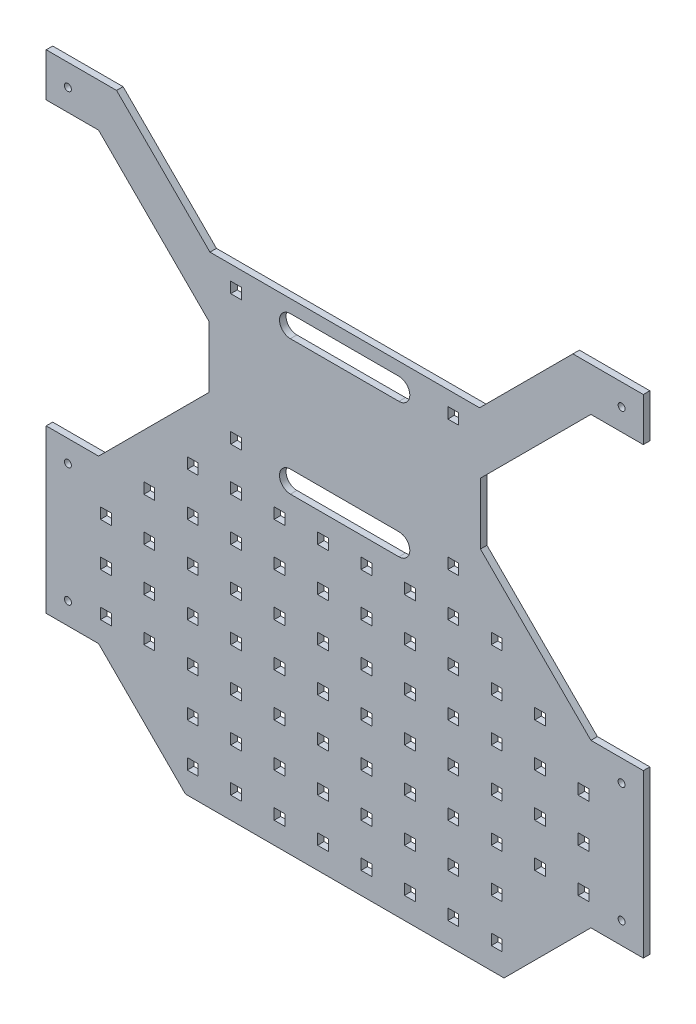
SolidWorks part; units mm, degrees
material "ABS"
ref_plane "Front Plane" through (0, 0, 0) normal (0, 0, 1) x (1, 0, 0)
ref_plane "Top Plane" through (0, 0, 0) normal (0, 1, 0) x (1, 0, 0)
ref_plane "Right Plane" through (0, 0, 0) normal (1, 0, 0) x (0, 0, -1)
sketch "Sketch1" plane through (0, 0, 0) normal (0, 0, 1) x (1, 0, 0)
  line L0 (-21.5101, 357.497) -> (2.6321, 357.497)
  line L1 (-21.5101, 592.497) -> (-21.5101, 302.497) construction
  line L2 (-21.5101, 442.2845) -> (-1.5101, 442.2845) construction
  line L3 (2.6321, 357.497) -> (53.4899, 306.6392)
  line L4 (185.9899, 432.2845) -> (165.9899, 412.2845)
  line L5 (43.4899, 292.497) -> (188.4899, 292.497) construction
  line L6 (43.4899, 282.497) -> (43.4899, 302.497) construction
  line L7 (188.4899, 302.497) -> (188.4899, 282.497) construction
  line L8 (115.9899, 412.2845) -> (115.9899, 208.7129) construction
  line L9 (53.4899, 306.6392) -> (53.4899, 278.3549)
  line L10 (-21.5101, 357.497) -> (-21.5101, 432.2845)
  line L11 (-21.5101, 432.2845) -> (45.9899, 432.2845)
  line L12 (45.9899, 432.2845) -> (65.9899, 412.2845)
  line L13 (65.9899, 412.2845) -> (165.9899, 412.2845)
  line L14 (-1.5101, 347.497) -> (-180.6113, 347.497) construction
  line L15 (43.4899, 302.497) -> (-1.5101, 347.497) construction
  line L16 (253.4899, 432.2845) -> (185.9899, 432.2845)
  line L17 (253.4899, 357.497) -> (253.4899, 432.2845)
  line L18 (178.4899, 306.6392) -> (178.4899, 278.3549)
  line L19 (229.3478, 357.497) -> (178.4899, 306.6392)
  line L20 (253.4899, 357.497) -> (229.3478, 357.497)
  line L21 (253.4899, 227.497) -> (229.3478, 227.497)
  line L22 (229.3478, 227.497) -> (178.4899, 278.3549)
  line L23 (253.4899, 227.497) -> (253.4899, 152.7096)
  line L24 (253.4899, 152.7096) -> (229.3478, 152.7096)
  line L27 (-21.5101, 152.7096) -> (2.6321, 152.7096)
  line L28 (-21.5101, 227.497) -> (-21.5101, 152.7096)
  line L30 (2.6321, 227.497) -> (53.4899, 278.3549)
  line L31 (-21.5101, 227.497) -> (2.6321, 227.497)
  line L32 (2.6321, 152.7096) -> (42.6321, 112.7096)
  line L33 (42.6321, 112.7096) -> (189.3478, 112.7096)
  line L34 (189.3478, 112.7096) -> (229.3478, 152.7096)
  line L35 (2.6321, 152.7096) -> (2.6321, 432.2845) construction
  line L36 (229.3478, 152.7096) -> (229.3478, 432.2845) construction
  point P39 (178.4899, 292.497)
  point P47 (53.4899, 292.497)
  dimension "D1" = 10
  dimension "D2" = 10
  dimension "D3" = 10
  dimension "D4" = 10
  dimension "D5" = 20
  dimension "D6" = 50
  dimension "D7" = 72.5
  dimension "D8" = 45
  dimension "D9" = 45
  dimension "D10" = 40
extrude "Extrude1" add sketch "Sketch1" along normal blind 3
sketch "Sketch3" plane through (0, 0, 3) normal (0, 0, 1) x (1, 0, 0)
  line L0 (43.4899, 292.497) -> (188.4899, 292.497) construction
  line L1 (43.4899, 282.497) -> (43.4899, 302.497) construction
  line L2 (188.4899, 302.497) -> (188.4899, 282.497) construction
  line L3 (90.9488, 323.497) -> (140.9488, 323.497) construction
  line L4 (90.9488, 328.497) -> (140.9488, 328.497)
  line L5 (90.9488, 318.497) -> (140.9488, 318.497)
  line L6 (90.9488, 261.497) -> (140.9488, 261.497) construction
  line L7 (90.9488, 256.497) -> (140.9488, 256.497)
  line L8 (90.9488, 266.497) -> (140.9488, 266.497)
  arc A0 (90.9488, 328.497) -> (90.9488, 318.497) centre (90.9488, 323.497) ccw
  arc A1 (140.9488, 318.497) -> (140.9488, 328.497) centre (140.9488, 323.497) ccw
  arc A2 (90.9488, 256.497) -> (90.9488, 266.497) centre (90.9488, 261.497) cw
  arc A3 (140.9488, 266.497) -> (140.9488, 256.497) centre (140.9488, 261.497) cw
  point P8 (115.9488, 323.497)
  point P15 (115.9488, 261.497)
  dimension "D3" = 5
  dimension "D1" = 31
  dimension "D2" = 50
extrude "Cut-Extrude2" cut sketch "Sketch3" against normal blind 3
sketch "Sketch5" plane through (0, 0, 0) normal (0, 0, -1) x (-1, 0, 0)
  line L0 (-253.4899, 377.497) -> (-221.0635, 377.497)
  line L1 (-253.4899, 357.497) -> (-253.4899, 432.2845) construction
  line L2 (-221.0635, 377.497) -> (-178.0635, 334.497)
  line L3 (-178.0635, 334.497) -> (-53.9163, 334.497)
  line L4 (-53.9163, 334.497) -> (-10.9163, 377.497)
  line L5 (-10.9163, 377.497) -> (21.5101, 377.497)
  line L6 (21.5101, 432.2845) -> (21.5101, 357.497) construction
  line L7 (-229.3478, 357.497) -> (-253.4899, 357.497) construction
  line L8 (-178.4899, 306.6392) -> (-229.3478, 357.497) construction
  line L9 (-2.6321, 357.497) -> (-53.4899, 306.6392) construction
  line L10 (21.5101, 357.497) -> (-2.6321, 357.497) construction
  line L11 (-90.9488, 318.497) -> (-140.9488, 318.497) construction
  line L12 (-253.4899, 377.497) -> (-253.4899, 432.2845)
  line L13 (-253.4899, 432.2845) -> (21.5101, 432.2845)
  line L14 (21.5101, 432.2845) -> (21.5101, 377.497)
  dimension "D1" = 20
  dimension "D2" = 20
  dimension "D3" = 20
  dimension "D4" = 20
  dimension "D5" = 16
extrude "Extrude3" cut sketch "Sketch5" against normal blind 10
sketch "Sketch6" plane through (0, 0, 3) normal (0, 0, 1) x (1, 0, 0)
  line L0 (-11.5101, 377.497) -> (-11.5101, 152.7096) construction
  line L1 (10.9163, 377.497) -> (-21.5101, 377.497) construction
  line L2 (-21.5101, 152.7096) -> (2.6321, 152.7096) construction
  line L3 (115.9899, 334.497) -> (115.9899, 112.7096) construction
  line L4 (178.0635, 334.497) -> (53.9163, 334.497) construction
  line L5 (42.6321, 112.7096) -> (189.3478, 112.7096) construction
  line L6 (2.6321, 227.497) -> (-21.5101, 227.497) construction
  line L7 (-21.5101, 227.497) -> (-21.5101, 152.7096) construction
  circle A0 centre (-11.5101, 367.497) radius 1.6
  circle A1 centre (-11.5101, 217.497) radius 1.6
  circle A2 centre (-11.5101, 162.7096) radius 1.6
  circle A3 centre (243.4899, 162.7096) radius 1.6
  circle A4 centre (243.4899, 217.497) radius 1.6
  circle A5 centre (243.4899, 367.497) radius 1.6
  dimension "D1" = 10
  dimension "D2" = 10
  dimension "D3" = 10
  dimension "D4" = 3.2
  dimension "D5" = 10
extrude "Extrude4" cut sketch "Sketch6" against normal blind 50
sketch "Sketch7" plane through (0, 0, 3) normal (0, 0, 1) x (1, 0, 0)
  line L10 (43.4899, 127.7096) -> (48.4899, 127.7096)
  line L11 (43.4899, 127.7096) -> (43.4899, 122.7096)
  line L12 (43.4899, 122.7096) -> (48.4899, 122.7096)
  line L13 (48.4899, 127.7096) -> (48.4899, 122.7096)
  line L14 (63.4899, 127.7096) -> (68.4899, 127.7096)
  line L15 (63.4899, 127.7096) -> (63.4899, 122.7096)
  line L16 (63.4899, 122.7096) -> (68.4899, 122.7096)
  line L17 (68.4899, 127.7096) -> (68.4899, 122.7096)
  line L18 (83.4899, 127.7096) -> (88.4899, 127.7096)
  line L19 (83.4899, 127.7096) -> (83.4899, 122.7096)
  line L20 (83.4899, 122.7096) -> (88.4899, 122.7096)
  line L21 (88.4899, 127.7096) -> (88.4899, 122.7096)
  line L22 (103.4899, 127.7096) -> (108.4899, 127.7096)
  line L23 (103.4899, 127.7096) -> (103.4899, 122.7096)
  line L24 (103.4899, 122.7096) -> (108.4899, 122.7096)
  line L25 (108.4899, 127.7096) -> (108.4899, 122.7096)
  line L26 (123.4899, 127.7096) -> (128.4899, 127.7096)
  line L27 (123.4899, 127.7096) -> (123.4899, 122.7096)
  line L28 (123.4899, 122.7096) -> (128.4899, 122.7096)
  line L29 (128.4899, 127.7096) -> (128.4899, 122.7096)
  line L30 (143.4899, 127.7096) -> (148.4899, 127.7096)
  line L31 (143.4899, 127.7096) -> (143.4899, 122.7096)
  line L32 (143.4899, 122.7096) -> (148.4899, 122.7096)
  line L33 (148.4899, 127.7096) -> (148.4899, 122.7096)
  line L34 (163.4899, 127.7096) -> (168.4899, 127.7096)
  line L35 (163.4899, 127.7096) -> (163.4899, 122.7096)
  line L36 (163.4899, 122.7096) -> (168.4899, 122.7096)
  line L37 (168.4899, 127.7096) -> (168.4899, 122.7096)
  line L38 (183.4899, 127.7096) -> (188.4899, 127.7096)
  line L39 (183.4899, 127.7096) -> (183.4899, 122.7096)
  line L40 (183.4899, 122.7096) -> (188.4899, 122.7096)
  line L41 (188.4899, 127.7096) -> (188.4899, 122.7096)
  line L54 (43.4899, 147.7096) -> (48.4899, 147.7096)
  line L55 (43.4899, 147.7096) -> (43.4899, 142.7096)
  line L56 (43.4899, 142.7096) -> (48.4899, 142.7096)
  line L57 (48.4899, 147.7096) -> (48.4899, 142.7096)
  line L58 (63.4899, 147.7096) -> (68.4899, 147.7096)
  line L59 (63.4899, 147.7096) -> (63.4899, 142.7096)
  line L60 (63.4899, 142.7096) -> (68.4899, 142.7096)
  line L61 (68.4899, 147.7096) -> (68.4899, 142.7096)
  line L62 (83.4899, 147.7096) -> (88.4899, 147.7096)
  line L63 (83.4899, 147.7096) -> (83.4899, 142.7096)
  line L64 (83.4899, 142.7096) -> (88.4899, 142.7096)
  line L65 (88.4899, 147.7096) -> (88.4899, 142.7096)
  line L66 (103.4899, 147.7096) -> (108.4899, 147.7096)
  line L67 (103.4899, 147.7096) -> (103.4899, 142.7096)
  line L68 (103.4899, 142.7096) -> (108.4899, 142.7096)
  line L69 (108.4899, 147.7096) -> (108.4899, 142.7096)
  line L70 (123.4899, 147.7096) -> (128.4899, 147.7096)
  line L71 (123.4899, 147.7096) -> (123.4899, 142.7096)
  line L72 (123.4899, 142.7096) -> (128.4899, 142.7096)
  line L73 (128.4899, 147.7096) -> (128.4899, 142.7096)
  line L74 (143.4899, 147.7096) -> (148.4899, 147.7096)
  line L75 (143.4899, 147.7096) -> (143.4899, 142.7096)
  line L76 (143.4899, 142.7096) -> (148.4899, 142.7096)
  line L77 (148.4899, 147.7096) -> (148.4899, 142.7096)
  line L78 (163.4899, 147.7096) -> (168.4899, 147.7096)
  line L79 (163.4899, 147.7096) -> (163.4899, 142.7096)
  line L80 (163.4899, 142.7096) -> (168.4899, 142.7096)
  line L81 (168.4899, 147.7096) -> (168.4899, 142.7096)
  line L82 (183.4899, 147.7096) -> (188.4899, 147.7096)
  line L83 (183.4899, 147.7096) -> (183.4899, 142.7096)
  line L84 (183.4899, 142.7096) -> (188.4899, 142.7096)
  line L85 (188.4899, 147.7096) -> (188.4899, 142.7096)
  line L94 (23.4899, 167.7096) -> (28.4899, 167.7096)
  line L95 (23.4899, 167.7096) -> (23.4899, 162.7096)
  line L96 (23.4899, 162.7096) -> (28.4899, 162.7096)
  line L97 (28.4899, 167.7096) -> (28.4899, 162.7096)
  line L98 (43.4899, 167.7096) -> (48.4899, 167.7096)
  line L99 (43.4899, 167.7096) -> (43.4899, 162.7096)
  line L100 (43.4899, 162.7096) -> (48.4899, 162.7096)
  line L101 (48.4899, 167.7096) -> (48.4899, 162.7096)
  line L102 (63.4899, 167.7096) -> (68.4899, 167.7096)
  line L103 (63.4899, 167.7096) -> (63.4899, 162.7096)
  line L104 (63.4899, 162.7096) -> (68.4899, 162.7096)
  line L105 (68.4899, 167.7096) -> (68.4899, 162.7096)
  line L106 (83.4899, 167.7096) -> (88.4899, 167.7096)
  line L107 (83.4899, 167.7096) -> (83.4899, 162.7096)
  line L108 (83.4899, 162.7096) -> (88.4899, 162.7096)
  line L109 (88.4899, 167.7096) -> (88.4899, 162.7096)
  line L110 (103.4899, 167.7096) -> (108.4899, 167.7096)
  line L111 (103.4899, 167.7096) -> (103.4899, 162.7096)
  line L112 (103.4899, 162.7096) -> (108.4899, 162.7096)
  line L113 (108.4899, 167.7096) -> (108.4899, 162.7096)
  line L114 (123.4899, 167.7096) -> (128.4899, 167.7096)
  line L115 (123.4899, 167.7096) -> (123.4899, 162.7096)
  line L116 (123.4899, 162.7096) -> (128.4899, 162.7096)
  line L117 (128.4899, 167.7096) -> (128.4899, 162.7096)
  line L118 (143.4899, 167.7096) -> (148.4899, 167.7096)
  line L119 (143.4899, 167.7096) -> (143.4899, 162.7096)
  line L120 (143.4899, 162.7096) -> (148.4899, 162.7096)
  line L121 (148.4899, 167.7096) -> (148.4899, 162.7096)
  line L122 (163.4899, 167.7096) -> (168.4899, 167.7096)
  line L123 (163.4899, 167.7096) -> (163.4899, 162.7096)
  line L124 (163.4899, 162.7096) -> (168.4899, 162.7096)
  line L125 (168.4899, 167.7096) -> (168.4899, 162.7096)
  line L126 (183.4899, 167.7096) -> (188.4899, 167.7096)
  line L127 (183.4899, 167.7096) -> (183.4899, 162.7096)
  line L128 (183.4899, 162.7096) -> (188.4899, 162.7096)
  line L129 (188.4899, 167.7096) -> (188.4899, 162.7096)
  line L130 (203.4899, 167.7096) -> (208.4899, 167.7096)
  line L131 (203.4899, 167.7096) -> (203.4899, 162.7096)
  line L132 (203.4899, 162.7096) -> (208.4899, 162.7096)
  line L133 (208.4899, 167.7096) -> (208.4899, 162.7096)
  line L134 (223.4899, 167.7096) -> (228.4899, 167.7096)
  line L135 (223.4899, 167.7096) -> (223.4899, 162.7096)
  line L136 (223.4899, 162.7096) -> (228.4899, 162.7096)
  line L137 (228.4899, 167.7096) -> (228.4899, 162.7096)
  line L138 (23.4899, 187.7096) -> (28.4899, 187.7096)
  line L139 (23.4899, 187.7096) -> (23.4899, 182.7096)
  line L140 (23.4899, 182.7096) -> (28.4899, 182.7096)
  line L141 (28.4899, 187.7096) -> (28.4899, 182.7096)
  line L142 (43.4899, 187.7096) -> (48.4899, 187.7096)
  line L143 (43.4899, 187.7096) -> (43.4899, 182.7096)
  line L144 (43.4899, 182.7096) -> (48.4899, 182.7096)
  line L145 (48.4899, 187.7096) -> (48.4899, 182.7096)
  line L146 (63.4899, 187.7096) -> (68.4899, 187.7096)
  line L147 (63.4899, 187.7096) -> (63.4899, 182.7096)
  line L148 (63.4899, 182.7096) -> (68.4899, 182.7096)
  line L149 (68.4899, 187.7096) -> (68.4899, 182.7096)
  line L150 (83.4899, 187.7096) -> (88.4899, 187.7096)
  line L151 (83.4899, 187.7096) -> (83.4899, 182.7096)
  line L152 (83.4899, 182.7096) -> (88.4899, 182.7096)
  line L153 (88.4899, 187.7096) -> (88.4899, 182.7096)
  line L154 (103.4899, 187.7096) -> (108.4899, 187.7096)
  line L155 (103.4899, 187.7096) -> (103.4899, 182.7096)
  line L156 (103.4899, 182.7096) -> (108.4899, 182.7096)
  line L157 (108.4899, 187.7096) -> (108.4899, 182.7096)
  line L158 (123.4899, 187.7096) -> (128.4899, 187.7096)
  line L159 (123.4899, 187.7096) -> (123.4899, 182.7096)
  line L160 (123.4899, 182.7096) -> (128.4899, 182.7096)
  line L161 (128.4899, 187.7096) -> (128.4899, 182.7096)
  line L162 (143.4899, 187.7096) -> (148.4899, 187.7096)
  line L163 (143.4899, 187.7096) -> (143.4899, 182.7096)
  line L164 (143.4899, 182.7096) -> (148.4899, 182.7096)
  line L165 (148.4899, 187.7096) -> (148.4899, 182.7096)
  line L166 (163.4899, 187.7096) -> (168.4899, 187.7096)
  line L167 (163.4899, 187.7096) -> (163.4899, 182.7096)
  line L168 (163.4899, 182.7096) -> (168.4899, 182.7096)
  line L169 (168.4899, 187.7096) -> (168.4899, 182.7096)
  line L170 (183.4899, 187.7096) -> (188.4899, 187.7096)
  line L171 (183.4899, 187.7096) -> (183.4899, 182.7096)
  line L172 (183.4899, 182.7096) -> (188.4899, 182.7096)
  line L173 (188.4899, 187.7096) -> (188.4899, 182.7096)
  line L174 (203.4899, 187.7096) -> (208.4899, 187.7096)
  line L175 (203.4899, 187.7096) -> (203.4899, 182.7096)
  line L176 (203.4899, 182.7096) -> (208.4899, 182.7096)
  line L177 (208.4899, 187.7096) -> (208.4899, 182.7096)
  line L178 (223.4899, 187.7096) -> (228.4899, 187.7096)
  line L179 (223.4899, 187.7096) -> (223.4899, 182.7096)
  line L180 (223.4899, 182.7096) -> (228.4899, 182.7096)
  line L181 (228.4899, 187.7096) -> (228.4899, 182.7096)
  line L182 (23.4899, 207.7096) -> (28.4899, 207.7096)
  line L183 (23.4899, 207.7096) -> (23.4899, 202.7096)
  line L184 (23.4899, 202.7096) -> (28.4899, 202.7096)
  line L185 (28.4899, 207.7096) -> (28.4899, 202.7096)
  line L186 (43.4899, 207.7096) -> (48.4899, 207.7096)
  line L187 (43.4899, 207.7096) -> (43.4899, 202.7096)
  line L188 (43.4899, 202.7096) -> (48.4899, 202.7096)
  line L189 (48.4899, 207.7096) -> (48.4899, 202.7096)
  line L190 (63.4899, 207.7096) -> (68.4899, 207.7096)
  line L191 (63.4899, 207.7096) -> (63.4899, 202.7096)
  line L192 (63.4899, 202.7096) -> (68.4899, 202.7096)
  line L193 (68.4899, 207.7096) -> (68.4899, 202.7096)
  line L194 (83.4899, 207.7096) -> (88.4899, 207.7096)
  line L195 (83.4899, 207.7096) -> (83.4899, 202.7096)
  line L196 (83.4899, 202.7096) -> (88.4899, 202.7096)
  line L197 (88.4899, 207.7096) -> (88.4899, 202.7096)
  line L198 (103.4899, 207.7096) -> (108.4899, 207.7096)
  line L199 (103.4899, 207.7096) -> (103.4899, 202.7096)
  line L200 (103.4899, 202.7096) -> (108.4899, 202.7096)
  line L201 (108.4899, 207.7096) -> (108.4899, 202.7096)
  line L202 (123.4899, 207.7096) -> (128.4899, 207.7096)
  line L203 (123.4899, 207.7096) -> (123.4899, 202.7096)
  line L204 (123.4899, 202.7096) -> (128.4899, 202.7096)
  line L205 (128.4899, 207.7096) -> (128.4899, 202.7096)
  line L206 (143.4899, 207.7096) -> (148.4899, 207.7096)
  line L207 (143.4899, 207.7096) -> (143.4899, 202.7096)
  line L208 (143.4899, 202.7096) -> (148.4899, 202.7096)
  line L209 (148.4899, 207.7096) -> (148.4899, 202.7096)
  line L210 (163.4899, 207.7096) -> (168.4899, 207.7096)
  line L211 (163.4899, 207.7096) -> (163.4899, 202.7096)
  line L212 (163.4899, 202.7096) -> (168.4899, 202.7096)
  line L213 (168.4899, 207.7096) -> (168.4899, 202.7096)
  line L214 (183.4899, 207.7096) -> (188.4899, 207.7096)
  line L215 (183.4899, 207.7096) -> (183.4899, 202.7096)
  line L216 (183.4899, 202.7096) -> (188.4899, 202.7096)
  line L217 (188.4899, 207.7096) -> (188.4899, 202.7096)
  line L218 (203.4899, 207.7096) -> (208.4899, 207.7096)
  line L219 (203.4899, 207.7096) -> (203.4899, 202.7096)
  line L220 (203.4899, 202.7096) -> (208.4899, 202.7096)
  line L221 (208.4899, 207.7096) -> (208.4899, 202.7096)
  line L222 (223.4899, 207.7096) -> (228.4899, 207.7096)
  line L223 (223.4899, 207.7096) -> (223.4899, 202.7096)
  line L224 (223.4899, 202.7096) -> (228.4899, 202.7096)
  line L225 (228.4899, 207.7096) -> (228.4899, 202.7096)
  line L226 (23.4899, 227.7096) -> (28.4899, 227.7096)
  line L227 (23.4899, 227.7096) -> (23.4899, 222.7096)
  line L228 (23.4899, 222.7096) -> (28.4899, 222.7096)
  line L229 (28.4899, 227.7096) -> (28.4899, 222.7096)
  line L230 (43.4899, 227.7096) -> (48.4899, 227.7096)
  line L231 (43.4899, 227.7096) -> (43.4899, 222.7096)
  line L232 (43.4899, 222.7096) -> (48.4899, 222.7096)
  line L233 (48.4899, 227.7096) -> (48.4899, 222.7096)
  line L234 (63.4899, 227.7096) -> (68.4899, 227.7096)
  line L235 (63.4899, 227.7096) -> (63.4899, 222.7096)
  line L236 (63.4899, 222.7096) -> (68.4899, 222.7096)
  line L237 (68.4899, 227.7096) -> (68.4899, 222.7096)
  line L238 (83.4899, 227.7096) -> (88.4899, 227.7096)
  line L239 (83.4899, 227.7096) -> (83.4899, 222.7096)
  line L240 (83.4899, 222.7096) -> (88.4899, 222.7096)
  line L241 (88.4899, 227.7096) -> (88.4899, 222.7096)
  line L242 (103.4899, 227.7096) -> (108.4899, 227.7096)
  line L243 (103.4899, 227.7096) -> (103.4899, 222.7096)
  line L244 (103.4899, 222.7096) -> (108.4899, 222.7096)
  line L245 (108.4899, 227.7096) -> (108.4899, 222.7096)
  line L246 (123.4899, 227.7096) -> (128.4899, 227.7096)
  line L247 (123.4899, 227.7096) -> (123.4899, 222.7096)
  line L248 (123.4899, 222.7096) -> (128.4899, 222.7096)
  line L249 (128.4899, 227.7096) -> (128.4899, 222.7096)
  line L250 (143.4899, 227.7096) -> (148.4899, 227.7096)
  line L251 (143.4899, 227.7096) -> (143.4899, 222.7096)
  line L252 (143.4899, 222.7096) -> (148.4899, 222.7096)
  line L253 (148.4899, 227.7096) -> (148.4899, 222.7096)
  line L254 (163.4899, 227.7096) -> (168.4899, 227.7096)
  line L255 (163.4899, 227.7096) -> (163.4899, 222.7096)
  line L256 (163.4899, 222.7096) -> (168.4899, 222.7096)
  line L257 (168.4899, 227.7096) -> (168.4899, 222.7096)
  line L258 (183.4899, 227.7096) -> (188.4899, 227.7096)
  line L259 (183.4899, 227.7096) -> (183.4899, 222.7096)
  line L260 (183.4899, 222.7096) -> (188.4899, 222.7096)
  line L261 (188.4899, 227.7096) -> (188.4899, 222.7096)
  line L262 (203.4899, 227.7096) -> (208.4899, 227.7096)
  line L263 (203.4899, 227.7096) -> (203.4899, 222.7096)
  line L264 (203.4899, 222.7096) -> (208.4899, 222.7096)
  line L265 (208.4899, 227.7096) -> (208.4899, 222.7096)
  line L274 (43.4899, 247.7096) -> (48.4899, 247.7096)
  line L275 (43.4899, 247.7096) -> (43.4899, 242.7096)
  line L276 (43.4899, 242.7096) -> (48.4899, 242.7096)
  line L277 (48.4899, 247.7096) -> (48.4899, 242.7096)
  line L278 (63.4899, 247.7096) -> (68.4899, 247.7096)
  line L279 (63.4899, 247.7096) -> (63.4899, 242.7096)
  line L280 (63.4899, 242.7096) -> (68.4899, 242.7096)
  line L281 (68.4899, 247.7096) -> (68.4899, 242.7096)
  line L282 (83.4899, 247.7096) -> (88.4899, 247.7096)
  line L283 (83.4899, 247.7096) -> (83.4899, 242.7096)
  line L284 (83.4899, 242.7096) -> (88.4899, 242.7096)
  line L285 (88.4899, 247.7096) -> (88.4899, 242.7096)
  line L286 (103.4899, 247.7096) -> (108.4899, 247.7096)
  line L287 (103.4899, 247.7096) -> (103.4899, 242.7096)
  line L288 (103.4899, 242.7096) -> (108.4899, 242.7096)
  line L289 (108.4899, 247.7096) -> (108.4899, 242.7096)
  line L290 (123.4899, 247.7096) -> (128.4899, 247.7096)
  line L291 (123.4899, 247.7096) -> (123.4899, 242.7096)
  line L292 (123.4899, 242.7096) -> (128.4899, 242.7096)
  line L293 (128.4899, 247.7096) -> (128.4899, 242.7096)
  line L294 (143.4899, 247.7096) -> (148.4899, 247.7096)
  line L295 (143.4899, 247.7096) -> (143.4899, 242.7096)
  line L296 (143.4899, 242.7096) -> (148.4899, 242.7096)
  line L297 (148.4899, 247.7096) -> (148.4899, 242.7096)
  line L298 (163.4899, 247.7096) -> (168.4899, 247.7096)
  line L299 (163.4899, 247.7096) -> (163.4899, 242.7096)
  line L300 (163.4899, 242.7096) -> (168.4899, 242.7096)
  line L301 (168.4899, 247.7096) -> (168.4899, 242.7096)
  line L302 (183.4899, 247.7096) -> (188.4899, 247.7096)
  line L303 (183.4899, 247.7096) -> (183.4899, 242.7096)
  line L304 (183.4899, 242.7096) -> (188.4899, 242.7096)
  line L305 (188.4899, 247.7096) -> (188.4899, 242.7096)
  line L322 (63.4899, 267.7096) -> (68.4899, 267.7096)
  line L323 (63.4899, 267.7096) -> (63.4899, 262.7096)
  line L324 (63.4899, 262.7096) -> (68.4899, 262.7096)
  line L325 (68.4899, 267.7096) -> (68.4899, 262.7096)
  line L342 (163.4899, 267.7096) -> (168.4899, 267.7096)
  line L343 (163.4899, 267.7096) -> (163.4899, 262.7096)
  line L344 (163.4899, 262.7096) -> (168.4899, 262.7096)
  line L345 (168.4899, 267.7096) -> (168.4899, 262.7096)
  line L454 (63.4899, 327.7096) -> (68.4899, 327.7096)
  line L455 (63.4899, 327.7096) -> (63.4899, 322.7096)
  line L456 (63.4899, 322.7096) -> (68.4899, 322.7096)
  line L457 (68.4899, 327.7096) -> (68.4899, 322.7096)
  line L474 (163.4899, 327.7096) -> (168.4899, 327.7096)
  line L475 (163.4899, 327.7096) -> (163.4899, 322.7096)
  line L476 (163.4899, 322.7096) -> (168.4899, 322.7096)
  line L477 (168.4899, 327.7096) -> (168.4899, 322.7096)
  line L494 (3.4899, 167.7096) -> (8.4899, 167.7096)
  line L495 (3.4899, 167.7096) -> (3.4899, 162.7096)
  line L496 (3.4899, 162.7096) -> (8.4899, 162.7096)
  line L497 (8.4899, 167.7096) -> (8.4899, 162.7096)
  line L498 (3.4899, 187.7096) -> (8.4899, 187.7096)
  line L499 (3.4899, 187.7096) -> (3.4899, 182.7096)
  line L500 (3.4899, 182.7096) -> (8.4899, 182.7096)
  line L501 (8.4899, 187.7096) -> (8.4899, 182.7096)
  line L502 (3.4899, 207.7096) -> (8.4899, 207.7096)
  line L503 (3.4899, 207.7096) -> (3.4899, 202.7096)
  line L504 (3.4899, 202.7096) -> (8.4899, 202.7096)
  line L505 (8.4899, 207.7096) -> (8.4899, 202.7096)
extrude "Extrude5" cut sketch "Sketch7" against normal blind 50
